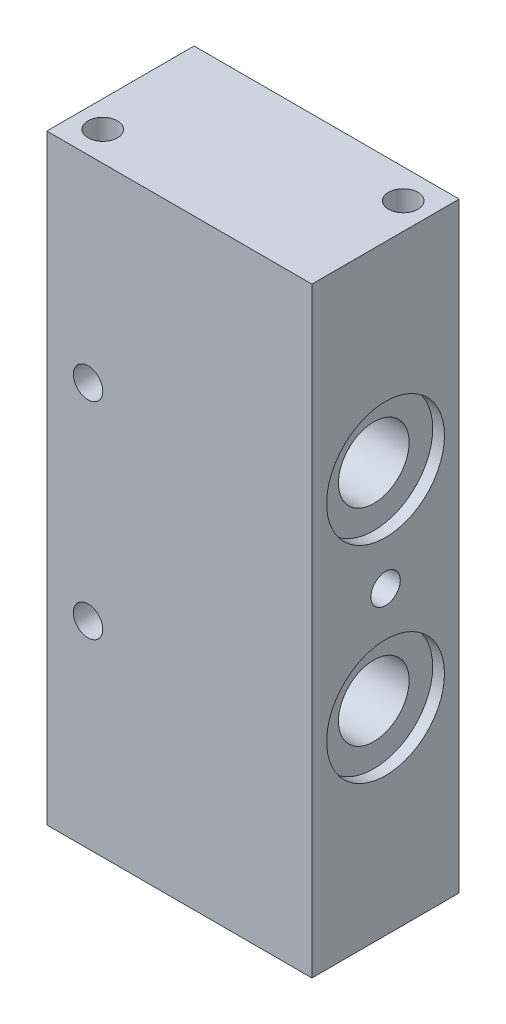
SolidWorks part; units mm, degrees
ref_plane "Front Plane" through (0, 0, 0) normal (0, 0, 1) x (1, 0, 0)
ref_plane "Top Plane" through (0, 0, 0) normal (0, 1, 0) x (1, 0, 0)
ref_plane "Right Plane" through (0, 0, 0) normal (1, 0, 0) x (0, 0, -1)
sketch "Sketch1" plane through (0, 0, 0) normal (0, 1, 0) x (1, 0, 0)
  line L1 (-22.5, 12.5) -> (22.5, 12.5)
  line L2 (-22.5, 12.5) -> (-22.5, -12.5)
  line L3 (-22.5, -12.5) -> (22.5, -12.5)
  line L4 (22.5, 12.5) -> (22.5, -12.5)
  line L5 (-22.5, 12.5) -> (22.5, -12.5) construction
  line L6 (-22.5, -12.5) -> (22.5, 12.5) construction
  point P0 (0, 0)
  dimension "D1" = 25
  dimension "D2" = 45
extrude "Boss-Extrude1" add sketch "Sketch1" along normal blind 70
sketch "Sketch2" plane through (22.5, 0, 0) normal (1, 0, 0) x (0, 0, -1)
  line L0 (-12.5, 70) -> (-12.5, 0) construction
  line L1 (-12.5, 70) -> (12.5, 70) construction
  line L2 (-12.5, 0) -> (12.5, 0) construction
  circle A0 centre (0, 52.5) radius 6
  circle A1 centre (0, 17.5) radius 6
  dimension "D1" = 12.5
  dimension "D3" = 17.5
  dimension "D2" = 17.5
extrude "Cut-Extrude1" cut sketch "Sketch2" against normal blind 70
sketch "Sketch3" plane through (22.5, 0, 0) normal (1, 0, 0) x (0, 0, -1)
  circle A0 centre (0, 17.5) radius 10
  circle A1 centre (0, 52.5) radius 10
extrude "Cut-Extrude2" cut sketch "Sketch3" against normal blind 2
sketch "Sketch4" plane through (-22.5, 0, 0) normal (-1, 0, 0) x (0, 0, 1)
  circle A0 centre (0, 52.5) radius 10
  circle A1 centre (0, 17.5) radius 10
extrude "Cut-Extrude3" cut sketch "Sketch4" against normal blind 2
sketch "Sketch5" plane through (22.5, 0, 0) normal (1, 0, 0) x (0, 0, -1)
  line L0 (-12.5, 70) -> (-12.5, 0) construction
  line L1 (12.5, 70) -> (12.5, 0) construction
  line L2 (-12.5, 70) -> (12.5, 70) construction
  line L3 (-12.5, 0) -> (12.5, 0) construction
  circle A0 centre (7.5, 6) radius 2.5
  circle A1 centre (-7.5, 6) radius 2.5
  circle A2 centre (7.5, 64) radius 2.5
  circle A3 centre (-7.5, 64) radius 2.5
  dimension "D1" = 5
  dimension "D2" = 5
  dimension "D3" = 6
  dimension "D4" = 6
  dimension "D5" = 6
  dimension "D6" = 6
  dimension "D7" = 5
  dimension "D8" = 5
extrude "Cut-Extrude4" cut sketch "Sketch5" against normal blind 15
sketch "Sketch6" plane through (22.5, 0, 0) normal (1, 0, 0) x (0, 0, -1)
  line L0 (-12.5, 70) -> (12.5, 70) construction
  circle A1 centre (0, 35) radius 2.5
  dimension "D1" = 35
extrude "Cut-Extrude5" cut sketch "Sketch6" against normal blind 15
sketch "Sketch7" plane through (0, 0, 12.5) normal (0, 0, 1) x (1, 0, 0)
  line L0 (-22.5, 70) -> (22.5, 70) construction
  line L1 (-22.5, 70) -> (-22.5, 0) construction
  line L2 (-22.5, 0) -> (22.5, 0) construction
  circle A0 centre (-15.5, 52.5) radius 2.5
  circle A1 centre (-15.5, 17.5) radius 2.5
  dimension "D1" = 17.5
  dimension "D3" = 17.5
  dimension "D2" = 7
  dimension "D4" = 7
extrude "Cut-Extrude6" cut sketch "Sketch7" against normal blind 36
sketch "Sketch8" plane through (0, 0, 12.5) normal (0, 0, 1) x (1, 0, 0)
  line L0 (-22.5, 0) -> (22.5, 0) construction
  line L1 (-22.5, 70) -> (22.5, 70) construction
  circle A0 centre (-15.5, 64) radius 2.5
  circle A1 centre (-15.5, 6) radius 2.5
  dimension "D1" = 6
  dimension "D2" = 6
extrude "Cut-Extrude7" cut sketch "Sketch8" against normal blind 38
sketch "Sketch9" plane through (0, 70, 0) normal (0, 1, 0) x (1, 0, 0)
  line L1 (-22.5, 12.5) -> (22.5, 12.5)
  line L2 (-22.5, 12.5) -> (-22.5, -12.5)
  line L3 (-22.5, -12.5) -> (22.5, -12.5)
  line L4 (22.5, 12.5) -> (22.5, -12.5)
extrude "Boss-Extrude2" add sketch "Sketch9" along normal blind 16
sketch "Sketch10" plane through (0, 0, 0) normal (0, -1, 0) x (1, 0, 0)
  line L1 (22.5, -12.5) -> (-22.5, -12.5)
  line L2 (22.5, -12.5) -> (22.5, 12.5)
  line L3 (22.5, 12.5) -> (-22.5, 12.5)
  line L4 (-22.5, -12.5) -> (-22.5, 12.5)
extrude "Boss-Extrude3" add sketch "Sketch10" along normal blind 16
sketch "Sketch11" plane through (0, 0, -12.5) normal (0, 0, -1) x (-1, 0, 0)
  circle A0 centre (15.5, 64) radius 2.5
  circle A1 centre (15.5, 6) radius 2.5
extrude "Boss-Extrude4" add sketch "Sketch11" against normal up to surface (25 mm away) up to face at (-13, 64, 12.5)
sketch "Sketch12" plane through (22.5, 0, 0) normal (1, 0, 0) x (0, 0, -1)
  circle A0 centre (-7.5, 64) radius 2.5
  circle A1 centre (7.5, 64) radius 2.5
  circle A2 centre (-7.5, 6) radius 2.5
  circle A3 centre (7.5, 6) radius 2.5
extrude "Boss-Extrude5" add sketch "Sketch12" against normal blind 27
sketch "Sketch13" plane through (0, 86, 0) normal (0, 1, 0) x (1, 0, 0)
  line L0 (22.5, -12.5) -> (22.5, 12.5) construction
  line L1 (22.5, 12.5) -> (-22.5, 12.5) construction
  line L2 (-22.5, 12.5) -> (-22.5, -12.5) construction
  line L3 (-22.5, -12.5) -> (22.5, -12.5) construction
  circle A0 centre (18, 7.5) radius 2.5
  circle A1 centre (-18, -7.5) radius 2.5
  point P6 (22.5, 0)
  point P9 (0, 12.5)
  point P12 (-22.5, 0)
  point P15 (0, -12.5)
  dimension "D1" = 7.5
  dimension "D2" = 18
  dimension "D3" = 7.5
  dimension "D4" = 18
extrude "Cut-Extrude8" cut sketch "Sketch13" against normal blind 14
